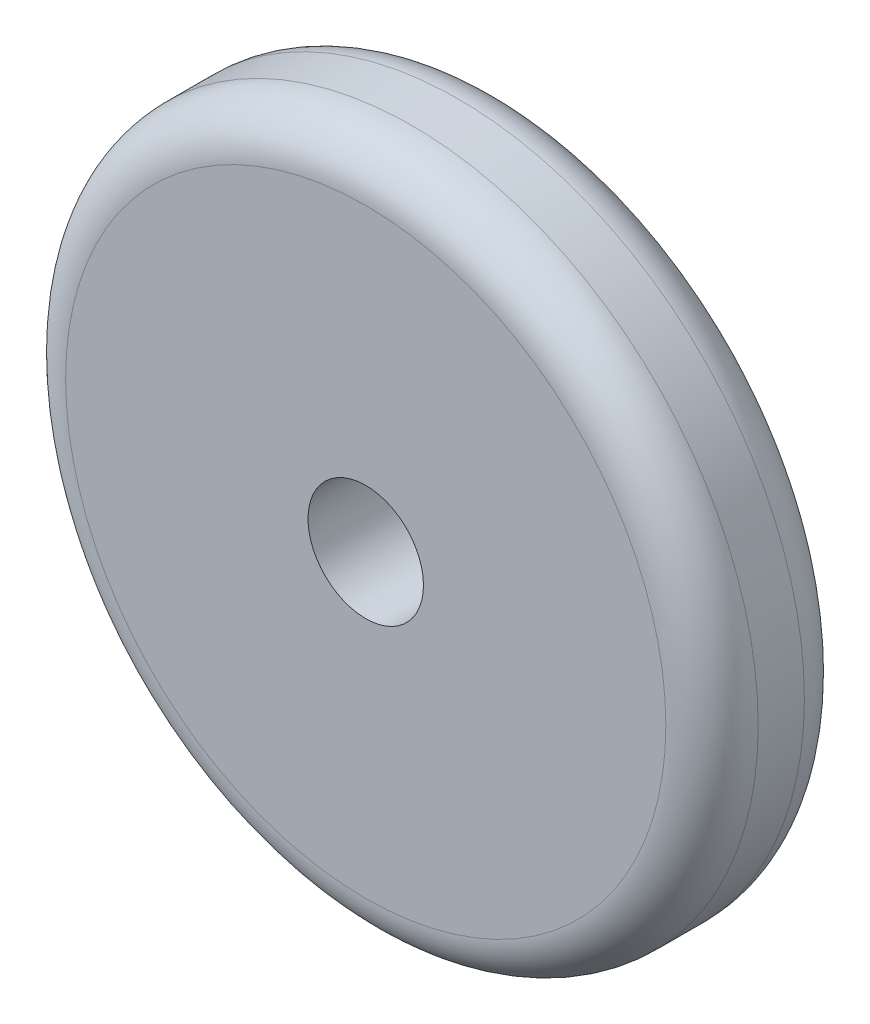
SolidWorks part; units mm, degrees
ref_plane "Alzado" through (0, 0, 0) normal (0, 0, 1) x (1, 0, 0)
ref_plane "Planta" through (0, 0, 0) normal (0, 1, 0) x (1, 0, 0)
ref_plane "Vista lateral" through (0, 0, 0) normal (1, 0, 0) x (0, 0, -1)
sketch "Croquis1" plane through (0, 0, 0) normal (0, 0, 1) x (1, 0, 0)
  circle A0 centre (0, 0) radius 15
  circle A1 centre (0, 0) radius 2.5
  dimension "D1" = 30
  dimension "D2" = 5
extrude "Saliente-Extruir1" add sketch "Croquis1" along normal blind 6
fillet "Redondeo1" radius 2 2 edges at (15, 0, 6) (15, 0, 0)
